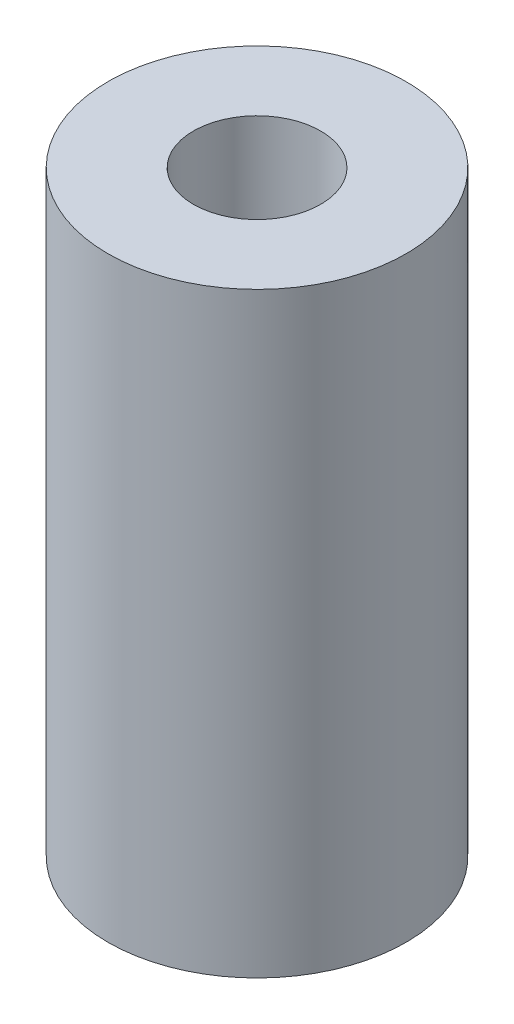
SolidWorks part; units mm, degrees
ref_plane "Front Plane" through (0, 0, 0) normal (0, 0, 1) x (1, 0, 0)
ref_plane "Top Plane" through (0, 0, 0) normal (0, 1, 0) x (1, 0, 0)
ref_plane "Right Plane" through (0, 0, 0) normal (1, 0, 0) x (0, 0, -1)
sketch "Sketch1" plane through (0, 0, 0) normal (0, 1, 0) x (1, 0, 0)
  circle A0 centre (0, 0) radius 4.064
  circle A1 centre (0, 0) radius 9.525
  dimension "D1" = 8.128
  dimension "D2" = 19.05
extrude "Boss-Extrude1" add sketch "Sketch1" along normal blind 38.1
